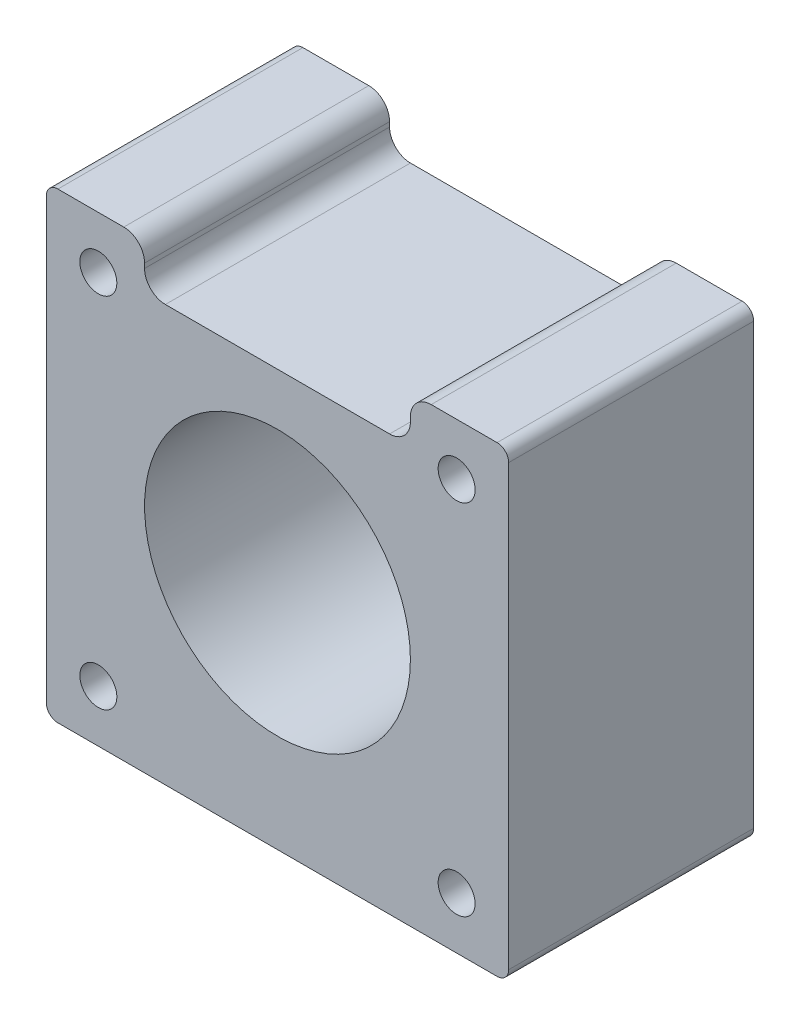
SolidWorks part; units mm, degrees
ref_plane "Front Plane" through (0, 0, 0) normal (0, 0, 1) x (1, 0, 0)
ref_plane "Top Plane" through (0, 0, 0) normal (0, 1, 0) x (1, 0, 0)
ref_plane "Right Plane" through (0, 0, 0) normal (1, 0, 0) x (0, 0, -1)
sketch "Sketch1" plane through (0, 0, 0) normal (0, 0, 1) x (1, 0, 0)
  line L0 (-20, 19) -> (-20, -19)
  line L1 (-15.5, -15.5) -> (15.5, -15.5) construction
  line L2 (-15.5, -15.5) -> (-15.5, 15.5) construction
  line L3 (-15.5, 15.5) -> (15.5, 15.5) construction
  line L4 (15.5, -15.5) -> (15.5, 15.5) construction
  line L5 (-15.5, -15.5) -> (15.5, 15.5) construction
  line L6 (-15.5, 15.5) -> (15.5, -15.5) construction
  line L7 (-19, -20) -> (19, -20)
  line L8 (20, 19) -> (20, -19)
  line L9 (-19, 20) -> (-13.3, 20)
  line L11 (-20, -20) -> (20, 20) construction
  line L12 (-20, 20) -> (20, -20) construction
  line L14 (13.3, 20) -> (19, 20)
  line L15 (-9.7, 16) -> (9.7, 16)
  line L16 (-11.5, 17.8) -> (-11.5, 18.2)
  line L18 (11.5, 17.8) -> (11.5, 18.2)
  circle A0 centre (0, 0) radius 11.5
  circle A1 centre (-15.5, 15.5) radius 1.6
  circle A2 centre (15.5, 15.5) radius 1.6
  circle A3 centre (15.5, -15.5) radius 1.6
  circle A4 centre (-15.5, -15.5) radius 1.6
  arc A5 (-20, -19) -> (-19, -20) centre (-19, -19) ccw
  arc A6 (19, -20) -> (20, -19) centre (19, -19) ccw
  arc A7 (20, 19) -> (19, 20) centre (19, 19) ccw
  arc A8 (-20, 19) -> (-19, 20) centre (-19, 19) cw
  arc A15 (-9.7, 16) -> (-11.5, 17.8) centre (-9.7, 17.8) cw
  arc A16 (11.5, 17.8) -> (9.7, 16) centre (9.7, 17.8) cw
  arc A17 (13.3, 20) -> (11.5, 18.2) centre (13.3, 18.2) ccw
  arc A18 (-13.3, 20) -> (-11.5, 18.2) centre (-13.3, 18.2) cw
  point P0 (0, 0)
  point P36 (-20, 6)
  point P43 (20, 6)
  point P44 (0, 20)
  dimension "D3" = 23
  dimension "D4" = 40
  dimension "D6" = 1
  dimension "D9" = 1.8
  dimension "D1" = 31
  dimension "D2" = 31
  dimension "D5" = 40
extrude "Boss-Extrude1" add sketch "Sketch1" along normal blind 21.2
sketch "Sketch2" plane through (0, 0, 21.2) normal (0, 0, 1) x (1, 0, 0)
  line L0 (20, -19) -> (20, 19) construction
  line L1 (-20, -5) -> (20, -5)
  line L2 (-20, -5) -> (-20, 5)
  line L3 (-20, 5) -> (20, 5)
  line L4 (20, -5) -> (20, 5)
  line L5 (-20, -5) -> (20, 5) construction
  line L6 (-20, 5) -> (20, -5) construction
  point P0 (0, 0)
  dimension "D1" = 10
extrude "Cut-Extrude1" [suppressed] cut sketch "Sketch2" against normal blind 1
